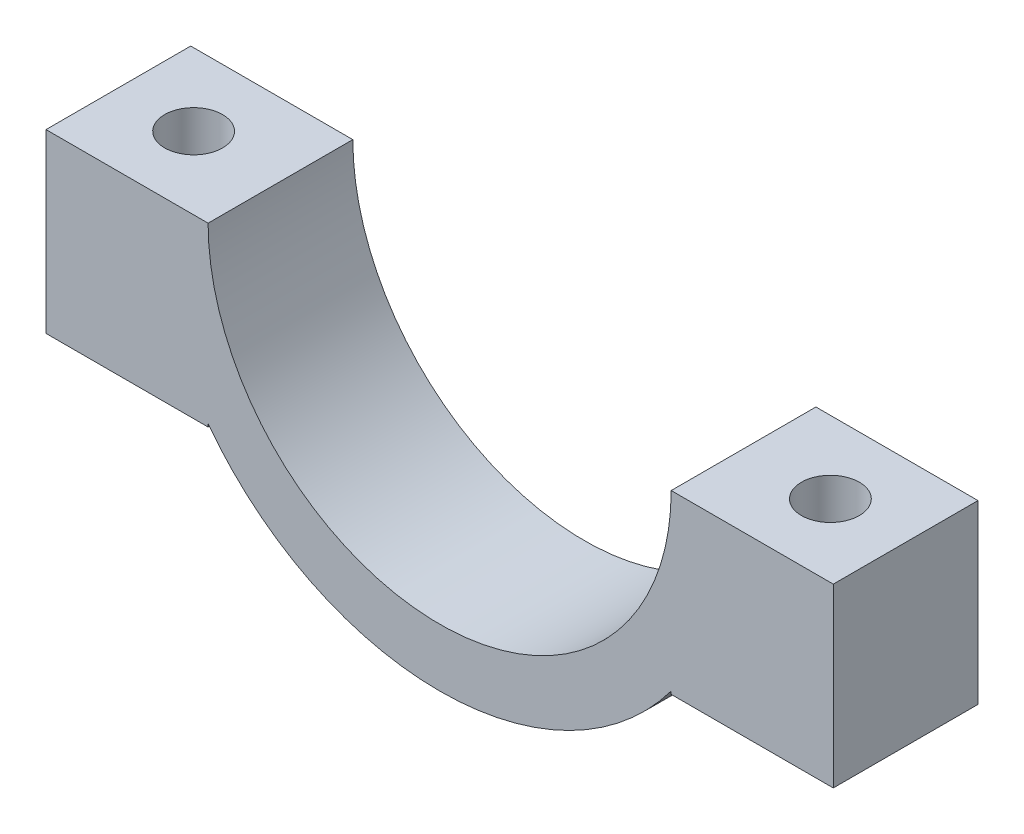
SolidWorks part; units mm, degrees
ref_plane "Front Plane" through (0, 0, 0) normal (0, 0, 1) x (1, 0, 0)
ref_plane "Top Plane" through (0, 0, 0) normal (0, 1, 0) x (1, 0, 0)
ref_plane "Right Plane" through (0, 0, 0) normal (1, 0, 0) x (0, 0, -1)
sketch "Sketch2" plane through (0, 0, 0) normal (0, 0, 1) x (1, 0, 0)
  line L0 (-1000, 0) -> (49000, 0) construction
  line L1 (-8, 0) -> (-13.6, 0)
  line L2 (-13.6, 0) -> (-13.6, 10)
  line L3 (-13.6, 10) -> (-8, 10)
  line L4 (-8, 10) -> (-8, 0)
  line L6 (8, 0) -> (13.6, 0)
  line L7 (13.6, 0) -> (13.6, 10)
  line L8 (13.6, 10) -> (8, 10)
  line L9 (8, 10) -> (8, 0)
  line L11 (-13.6, 0) -> (-8, 0)
  line L12 (-13.6, 0) -> (-13.6, -6.1)
  line L13 (-13.6, -6.1) -> (-8, -6.1)
  line L14 (-8, 0) -> (-8, -6.1)
  line L15 (13.6, 0) -> (8, 0)
  line L16 (13.6, 0) -> (13.6, -6.1)
  line L17 (13.6, -6.1) -> (8, -6.1)
  line L18 (8, 0) -> (8, -6.1)
  circle A0 centre (0, 0) radius 8
  circle A1 centre (0, 0) radius 10
  circle A2 centre (-5.5966, 11.6315) radius 2.9079
  circle A3 centre (5.6058, 11.6315) radius 2.9079
  spline S0 degree 1 poles (-8, 10) (0, 10) knots 0 0 1 1
  dimension "D1" = 16
  dimension "D2" = 20
  dimension "D5" = 10
  dimension "D3" = 5.6
  dimension "D4" = 10
  dimension "D6" = 5.6
  dimension "D7" = 6.1
  dimension "D8" = 6.1
extrude "Boss-Extrude1" add sketch "Sketch2" along normal blind 5 contours A1 L11 L12 L13 L14 | L1 A1 L14 | L14 A1 L18 A0 | L18 A1 L6 | A1 L18 L17 L16 L15
sketch "Sketch3" plane through (0, 0, 0) normal (0, 1, 0) x (1, 0, 0)
  circle A0 centre (-11, -2.5) radius 1
  circle A1 centre (11, -2.5) radius 1
  point P3 (-13, -2.5)
  dimension "D3" = 2
  dimension "D4" = 2
extrude "Cut-Extrude1" cut sketch "Sketch3" against normal blind 10
